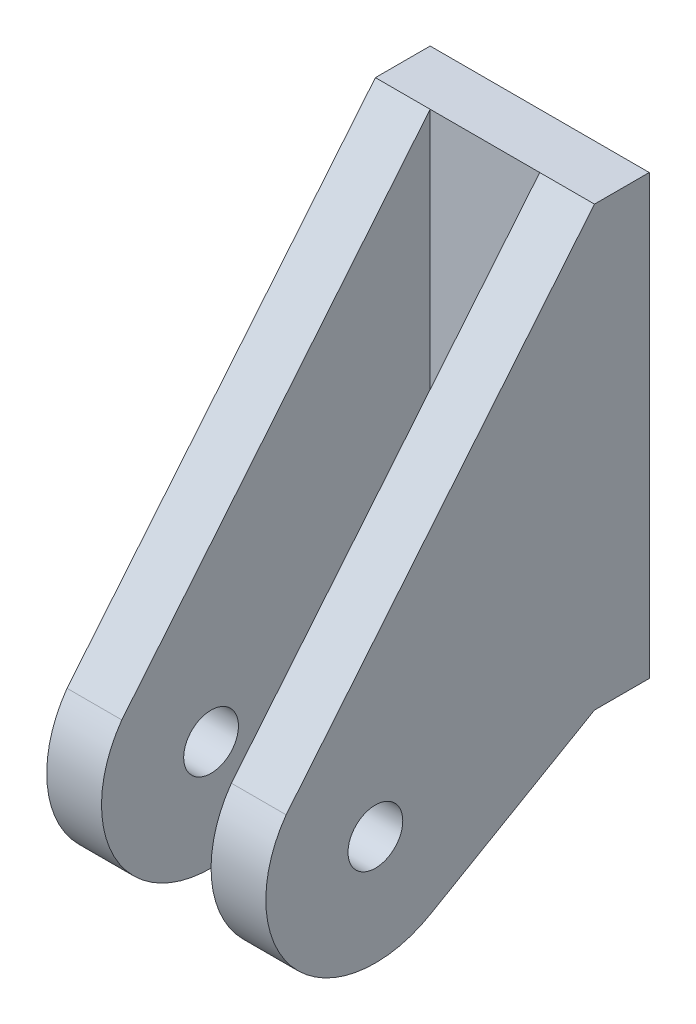
SolidWorks part; units mm, degrees
ref_plane "Front Plane" through (0, 0, 0) normal (0, 0, 1) x (1, 0, 0)
ref_plane "Top Plane" through (0, 0, 0) normal (0, 1, 0) x (1, 0, 0)
ref_plane "Right Plane" through (0, 0, 0) normal (1, 0, 0) x (0, 0, -1)
sketch "Sketch1" plane through (0, 0, 0) normal (0, 0, 1) x (1, 0, 0)
  line L1 (0, 0) -> (25.4, 0)
  line L2 (0, 0) -> (0, 50.8)
  line L3 (0, 50.8) -> (25.4, 50.8)
  line L4 (25.4, 0) -> (25.4, 50.8)
  dimension "D1" = 50.8
  dimension "D2" = 25.4
extrude "Boss-Extrude1" add sketch "Sketch1" along normal blind 6.35
sketch "Sketch2" plane through (25.4, 0, 0) normal (1, 0, 0) x (0, 0, -1)
  line L0 (-6.35, 0) -> (-100.9089, 0) construction
  line L1 (-6.35, 0) -> (-25.4, -10.9985)
  line L2 (-42.0974, 7.3635) -> (-6.35, 50.8)
  line L3 (-6.35, 50.8) -> (-6.35, 0)
  circle A0 centre (-31.75, 0) radius 3.175
  arc A1 (-25.4, -10.9985) -> (-42.0974, 7.3635) centre (-31.75, 0) cw
  point P6 (-42.0974, 7.3635)
  line M4 (-6.35, 50.8) -> (-6.35, 0)
  dimension "D1" = 6.35
  dimension "D3" = 12.7
  dimension "D2" = 25.4
extrude "Boss-Extrude2" add sketch "Sketch2" against normal blind 6.35 contours L0 L2 A1 A0 M4 | L1 L0 A0 A1
sketch "Sketch3" plane through (0, 0, 0) normal (-1, 0, 0) x (0, 0, 1)
  line L3 (6.35, 0) -> (25.4, -10.9985)
  line L4 (42.0974, 7.3635) -> (6.35, 50.8)
  line L5 (6.35, 50.8) -> (6.35, 0)
  line L6 (6.35, 0) -> (25.4, -10.9985)
  line L7 (42.0974, 7.3635) -> (6.35, 50.8)
  line L8 (6.35, 50.8) -> (6.35, 0)
  circle A0 centre (31.75, 0) radius 3.175 construction
  arc A1 (25.4, -10.9985) -> (42.0974, 7.3635) centre (31.75, 0) ccw
  arc A2 (25.4, -10.9985) -> (42.0974, 7.3635) centre (31.75, 0) ccw
  circle A3 centre (31.75, 0) radius 3.175
  line M7 (6.35, 0) -> (6.35, 50.8)
  dimension "D1" = 0
extrude "Boss-Extrude3" add sketch "Sketch3" against normal blind 6.35 contours L6 A2 L7 A3 M7
